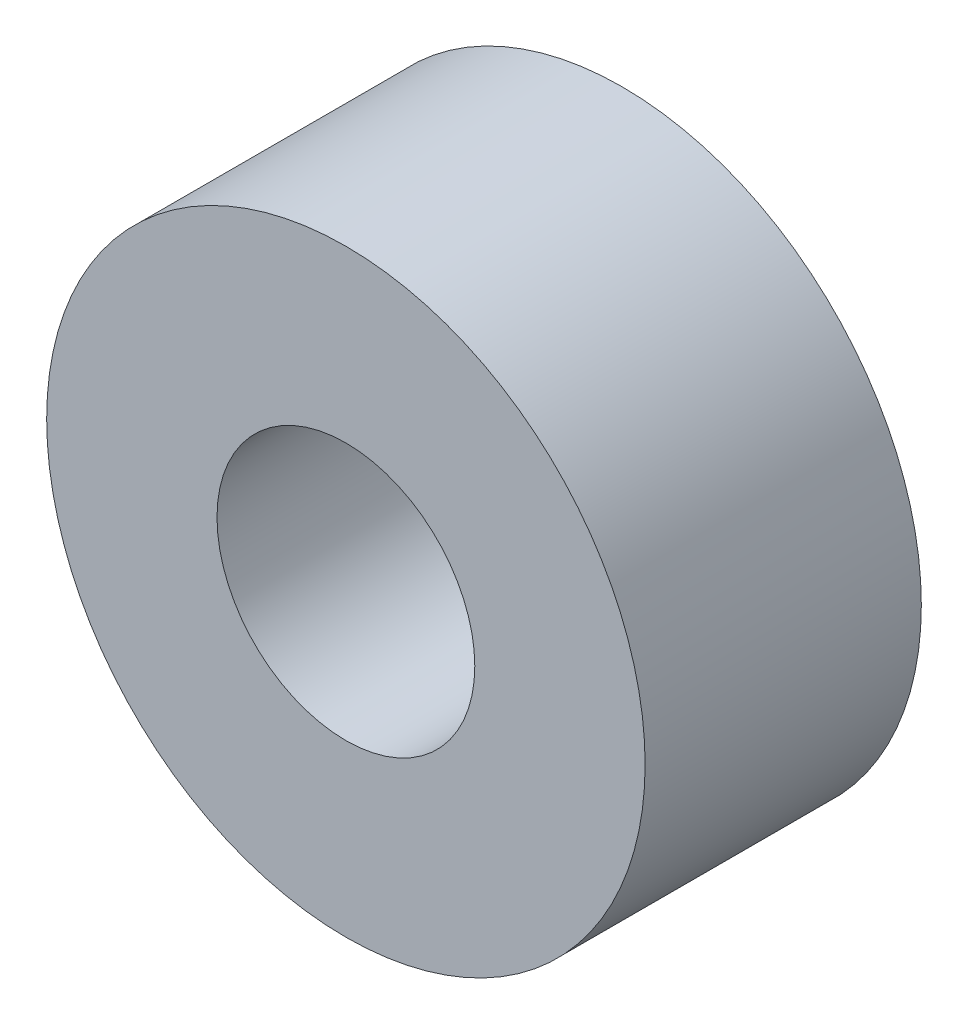
SolidWorks part; units mm, degrees
ref_plane "Plan de face" through (0, 0, 0) normal (0, 0, 1) x (1, 0, 0)
ref_plane "Plan de dessus" through (0, 0, 0) normal (0, 1, 0) x (1, 0, 0)
ref_plane "Plan de droite" through (0, 0, 0) normal (1, 0, 0) x (0, 0, -1)
sketch "Esquisse1" plane through (0, 0, 0) normal (0, 0, 1) x (1, 0, 0)
  circle A0 centre (0, 0) radius 3.25
  circle A1 centre (0, 0) radius 1.4
  dimension "D1" = 6.5
  dimension "D2" = 2.8
extrude "Boss.-Extru.1" add sketch "Esquisse1" along normal blind 3
